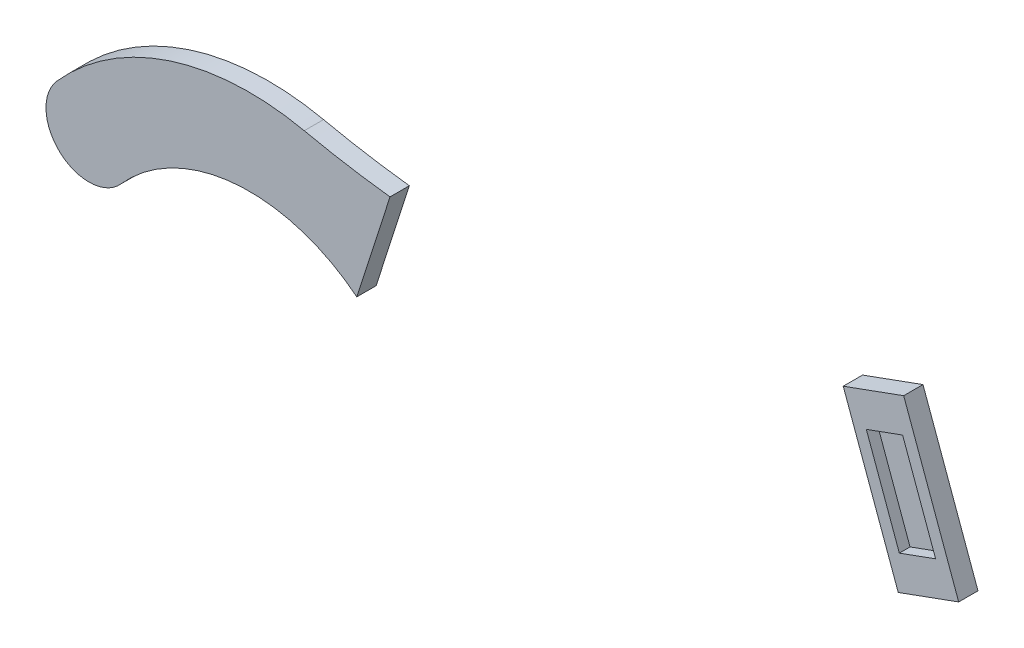
SolidWorks part; units mm, degrees
ref_plane "Спереди" through (0, 0, 0) normal (0, 0, 1) x (1, 0, 0)
ref_plane "Сверху" through (0, 0, 0) normal (0, 1, 0) x (1, 0, 0)
ref_plane "Справа" through (0, 0, 0) normal (1, 0, 0) x (0, 0, -1)
sketch "Sketch1" plane through (0, 0, 0) normal (0, 0, 1) x (1, 0, 0)
  line L0 (0, 0) -> (51.303, -140.9539)
  line L1 (-1000, 0) -> (49000, 0) construction
  line L2 (10.6418, 0) -> (119.8328, -300) construction
  line L3 (0, 0) -> (-93.9693, -34.202)
  line L4 (-458.1803, -350) -> (-59.8669, -350)
  line L5 (51.303, -140.9539) -> (-5.0785, -161.4751)
  circle A0 centre (119.8328, -300) radius 127.5 construction
  circle A1 centre (-610.1672, -300) radius 127.5 construction
  arc A3 (-458.1803, -350) -> (-729.9368, -193.9094) centre (-610.1672, -300) ccw
  arc A4 (-729.9368, -193.9094) -> (-789.8217, -140.864) centre (-759.8792, -167.3867) cw
  arc A5 (-789.8217, -140.864) -> (-559.0472, -65.5075) centre (-610.1672, -300) cw
  arc A6 (-559.0472, -65.5075) -> (-93.9693, -34.202) centre (-380.5645, 753.2118) ccw
  arc A7 (-59.8669, -350) -> (-5.0785, -161.4751) centre (119.8328, -300) cw
  dimension "D3" = 255
  dimension "D4" = 255
  dimension "D10" = 40
  dimension "D11" = 160
  dimension "D1" = 150
  dimension "D2" = 110
  dimension "D5" = 300
  dimension "D6" = 300
  dimension "D7" = 730
  dimension "D8" = 10
  dimension "D9" = 100
  dimension "D12" = 350
  dimension "D13" = 60
extrude "Boss-Extrude1" add sketch "Sketch1" along normal blind 18
sketch "Sketch2" plane through (0, 0, 18) normal (0, 0, 1) x (1, 0, 0)
  line L0 (-458.1803, -350) -> (-59.8669, -350) construction
  line L1 (-287.5083, -315) -> (-87.5083, -315)
  line L2 (-287.5083, -315) -> (-287.5083, -218)
  line L3 (-287.5083, -218) -> (-87.5083, -218)
  line L4 (-87.5083, -315) -> (-87.5083, -218)
  line L5 (-287.5083, -315) -> (-87.5083, -218) construction
  line L6 (-287.5083, -218) -> (-87.5083, -315) construction
  line L7 (-322.5083, -315) -> (-432.5083, -315)
  line L8 (-322.5083, -315) -> (-322.5083, -255)
  line L9 (-432.5083, -315) -> (-432.5083, -255)
  arc A0 (-432.5083, -255) -> (-322.5083, -255) centre (-377.5083, -255) cw
  point P0 (-187.5083, -266.5)
  dimension "D1" = 200
  dimension "D2" = 97
  dimension "D3" = 35
  dimension "D4" = 110
  dimension "D5" = 60
  dimension "D6" = 60
  dimension "D7" = 35
extrude "Cut-Extrude1" cut sketch "Sketch2" against normal through all
sketch "Sketch3" plane through (0, 0, 18) normal (0, 0, 1) x (1, 0, 0)
  line L0 (-1.0157, -32.295) -> (29.7661, -116.8674)
  line L1 (-1.0157, -32.295) -> (-34.8446, -44.6077)
  line L2 (29.7661, -116.8674) -> (-4.0628, -129.1801)
  line L3 (-34.8446, -44.6077) -> (-4.0628, -129.1801)
  line L5 (51.303, -140.9539) -> (0, 0) construction
  line L6 (0, 0) -> (-93.9693, -34.202) construction
  line L7 (-5.0785, -161.4751) -> (51.303, -140.9539) construction
  line L8 (-17.9302, -38.4514) -> (12.8516, -123.0237) construction
  dimension "D1" = 36
  dimension "D2" = 30
  dimension "D3" = 30
  dimension "D4" = 30
sketch "Sketch4" plane through (0, 0, 18) normal (0, 0, 1) x (1, 0, 0)
  line L0 (-5.0785, -161.4751) -> (-84.8267, 57.6311)
  line L1 (-84.8267, 57.6311) -> (-457.0925, -10.7647)
  line L2 (-457.0925, -10.7647) -> (-587.0406, -414.4861)
  line L3 (-587.0406, -414.4861) -> (5.9886, -394.516)
  line L4 (5.9886, -394.516) -> (-5.0785, -161.4751)
  line L5 (51.303, -140.9539) -> (0, 0) construction
extrude "Cut-Extrude2" cut sketch "Sketch4" against normal through all
extrude "Cut-Extrude3" cut sketch "Sketch3" against normal blind 10
